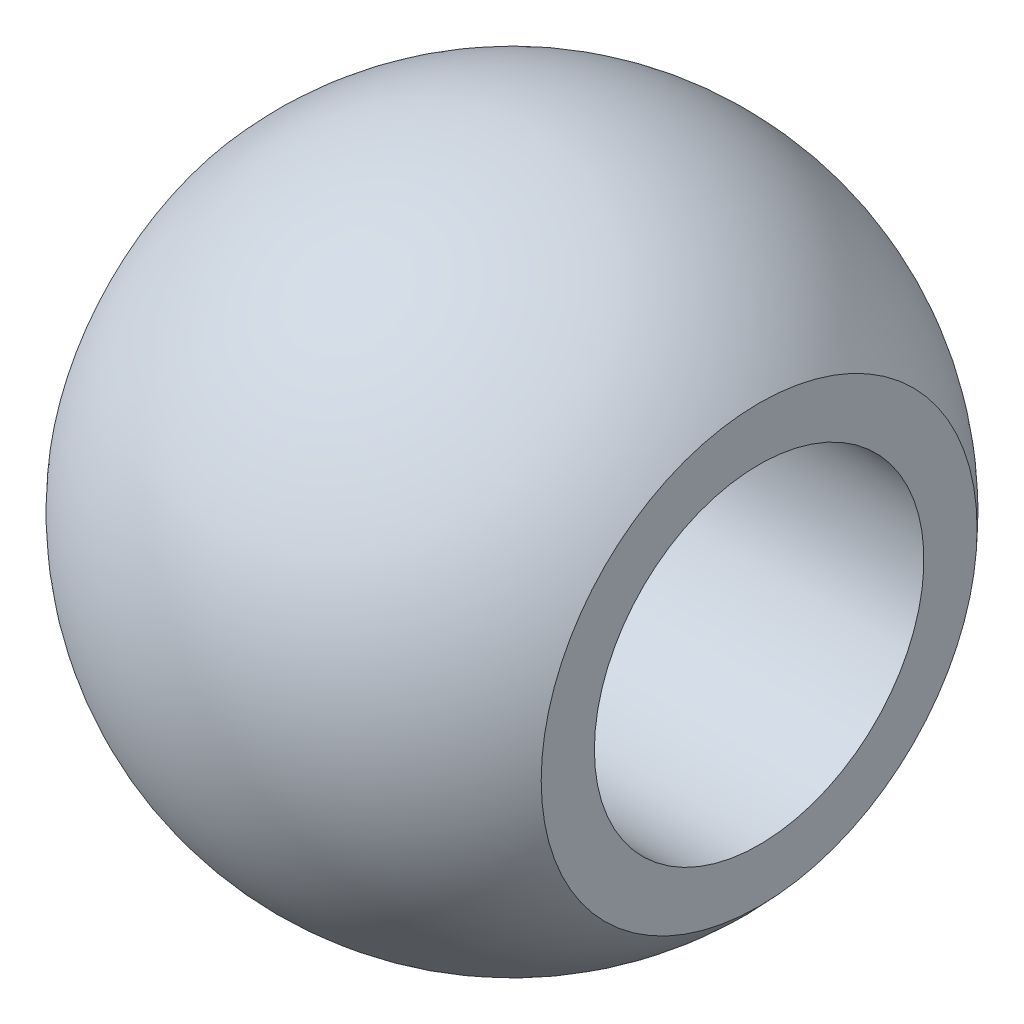
SolidWorks part; units mm, degrees
ref_plane "Front Plane" through (0, 0, 0) normal (0, 0, 1) x (1, 0, 0)
ref_plane "Top Plane" through (0, 0, 0) normal (0, 1, 0) x (1, 0, 0)
ref_plane "Right Plane" through (0, 0, 0) normal (1, 0, 0) x (0, 0, -1)
sketch "Sketch1" plane through (0, 0, 0) normal (0, 0, 1) x (1, 0, 0)
  line L0 (-16.6941, 0) -> (-10, 0) construction
  line L1 (-7.5, 0) -> (7.5, 0)
  line L2 (7.5, 0) -> (7.5, 6.6144)
  line L3 (-7.5, 0) -> (-7.5, 6.6144)
  line L4 (-7.5, 0) -> (7.5, 0) construction
  line L5 (10, 0) -> (17.4399, 0) construction
  line L6 (-10, 0) -> (10, 0) construction
  arc A0 (7.5, 6.6144) -> (-7.5, 6.6144) centre (0, 0) ccw
  point P5 (0, 0)
  dimension "D3" = 10
  dimension "D1" = 20
  dimension "D2" = 15
revolve "Revolve1" add sketch "Sketch1" angle 360 about L6
sketch "Sketch2" plane through (-7.5, 0, 0) normal (-1, 0, 0) x (0, 0, 1)
  circle A0 centre (0, 0) radius 5
  dimension "D1" = 10
extrude "Cut-Extrude1" cut sketch "Sketch2" against normal through all both and the other way through all
